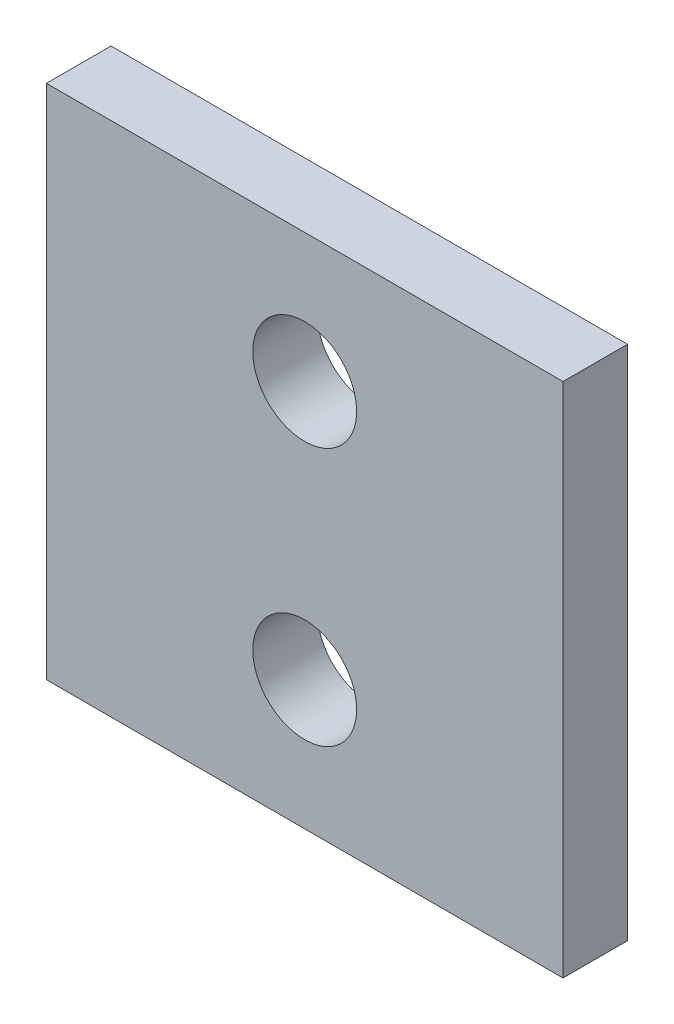
SolidWorks part; units mm, degrees
material "6063-T6"
ref_plane "Front" through (0, 0, 0) normal (0, 0, 1) x (1, 0, 0)
ref_plane "Top" through (0, 0, 0) normal (0, 1, 0) x (1, 0, 0)
ref_plane "Right" through (0, 0, 0) normal (1, 0, 0) x (0, 0, -1)
sketch "Sketch1" plane through (0, 0, 0) normal (0, 0, 1) x (1, 0, 0)
  line L1 (0, 0) -> (25.4, 0)
  line L2 (0, 0) -> (0, 25.4)
  line L3 (0, 25.4) -> (25.4, 25.4)
  line L4 (25.4, 0) -> (25.4, 25.4)
  line L5 (0, 0) -> (25.4, 25.4) construction
  line L6 (0, 25.4) -> (25.4, 0) construction
  point P4 (12.7, 12.7)
  dimension "D1" = 25.4
  dimension "D2" = 25.4
extrude "Boss-Extrude1" add sketch "Sketch1" along normal blind 3.175
sketch "Sketch2" plane through (0, 0, 0) normal (0, 0, -1) x (-1, 0, 0)
  line L0 (-12.7, 6.35) -> (-12.7, 0) construction
  line L1 (0, 0) -> (-25.4, 0) construction
  line L2 (-12.7, 19.05) -> (-12.7, 25.4) construction
  line L3 (-25.4, 25.4) -> (0, 25.4) construction
  circle A0 centre (-12.7, 6.35) radius 2.5527
  circle A1 centre (-12.7, 19.05) radius 2.5527
  dimension "D1" = 5.1054
  dimension "D2" = 5.1054
  dimension "D3" = 6.35
extrude "Cut-Extrude1" cut sketch "Sketch2" against normal up to next
